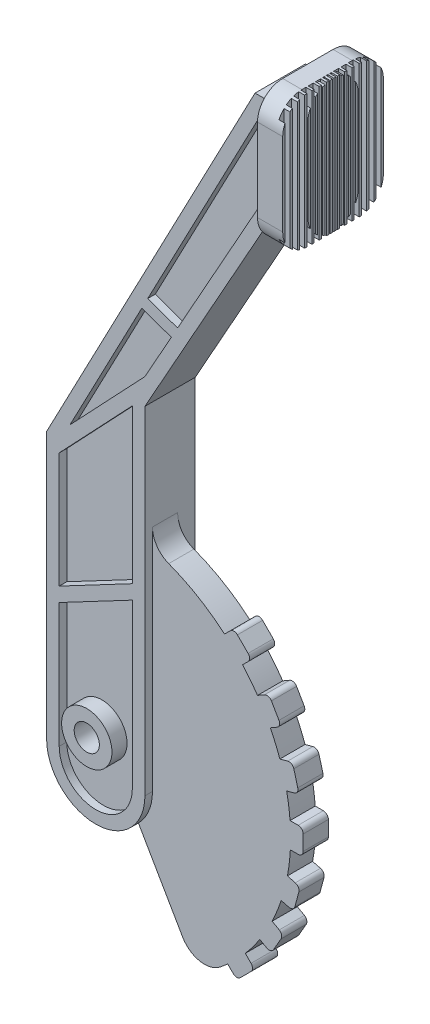
SolidWorks part; units mm, degrees
material "AISI Type 316L stainless steel"
ref_plane "Front Plane" through (0, 0, 0) normal (0, 0, 1) x (1, 0, 0)
ref_plane "Top Plane" through (0, 0, 0) normal (0, 1, 0) x (1, 0, 0)
ref_plane "Right Plane" through (0, 0, 0) normal (1, 0, 0) x (0, 0, -1)
sketch "Sketch1" plane through (0, 0, 0) normal (0, 0, 1) x (1, 0, 0)
  line L0 (0, 0) -> (0, 31.82)
  line L1 (0, 31.82) -> (-10.99, 31.82)
  line L2 (-93.795, -231.86) -> (-54.745, -231.86) construction
  line L3 (-93.795, -231.86) -> (-93.795, -126.01)
  line L4 (-93.795, -126.01) -> (-10.99, 31.82)
  line L5 (-54.745, -231.86) -> (-54.745, -97.84)
  line L6 (-54.745, -97.84) -> (0, 0)
  arc A0 (-93.795, -231.86) -> (-54.745, -231.86) centre (-74.27, -231.86) ccw
  dimension "D3" = 39.05
  dimension "D1" = 10.99
  dimension "D2" = 31.82
  dimension "D4" = 105.85
  dimension "D5" = 134.02
  dimension "D6" = 231.86
  dimension "D7" = 74.27
extrude "Boss-Extrude1" add sketch "Sketch1" along normal blind 10
sketch "Sketch2" plane through (0, 0, 0) normal (1, 0, 0) x (0, 0, -1)
  line L0 (-5, 0) -> (-5, 31.82) construction
  line L1 (-10, 0) -> (0, 0) construction
  line L2 (-10, 31.82) -> (0, 31.82) construction
  line L3 (-10, 15.91) -> (0, 15.91) construction
  line L4 (-10, 0) -> (-10, 31.82) construction
  line L5 (0, 0) -> (0, 31.82) construction
  line L7 (-10, -10.515) -> (0, -10.515)
  line L8 (-20, -0.515) -> (-20, 32.335)
  line L9 (-10, 42.335) -> (0, 42.335)
  line L10 (10, -0.515) -> (10, 32.335)
  line L11 (-20, -10.515) -> (10, 42.335) construction
  line L12 (-20, 42.335) -> (10, -10.515) construction
  arc A0 (0, -10.515) -> (10, -0.515) centre (0, -0.515) ccw
  arc A1 (-20, 32.335) -> (-10, 42.335) centre (-10, 32.335) cw
  arc A2 (-10, -10.515) -> (-20, -0.515) centre (-10, -0.515) cw
  arc A3 (0, 42.335) -> (10, 32.335) centre (0, 32.335) cw
  point P12 (-5, 15.91)
  point P29 (-5, -10.515)
  dimension "D1" = 10
  dimension "D2" = 52.85
  dimension "D3" = 30
extrude "Boss-Extrude2" add sketch "Sketch2" along normal blind 10
sketch "Sketch3" plane through (0, -10.515, 0) normal (0, -1, 0) x (1, 0, 0)
  line L0 (7.63, -4.1) -> (11.13, -4.1)
  line L1 (7.63, -7) -> (11.13, -7)
  line L2 (7.63, -7) -> (7.63, -9)
  line L3 (7.63, -9) -> (11.13, -9)
  line L4 (11.13, -7) -> (11.13, -9)
  line L5 (7.63, -7) -> (11.13, -9) construction
  line L6 (7.63, -9) -> (11.13, -7) construction
  line L7 (11.13, -4.1) -> (11.13, -6.1)
  line L8 (7.63, -6.1) -> (11.13, -6.1)
  line L9 (7.63, -4.1) -> (7.63, -6.1)
  line L10 (7.63, -1.2) -> (11.13, -1.2)
  line L11 (11.13, -1.2) -> (11.13, -3.2)
  line L12 (7.63, -3.2) -> (11.13, -3.2)
  line L13 (7.63, -1.2) -> (7.63, -3.2)
  line L14 (7.63, 1.7) -> (11.13, 1.7)
  line L15 (11.13, 1.7) -> (11.13, -0.3)
  line L16 (7.63, -0.3) -> (11.13, -0.3)
  line L17 (7.63, 1.7) -> (7.63, -0.3)
  line L18 (7.63, 4.6) -> (11.13, 4.6)
  line L19 (11.13, 4.6) -> (11.13, 2.6)
  line L20 (7.63, 2.6) -> (11.13, 2.6)
  line L21 (7.63, 4.6) -> (7.63, 2.6)
  line L22 (7.63, 7.5) -> (11.13, 7.5)
  line L23 (11.13, 7.5) -> (11.13, 5.5)
  line L24 (7.63, 5.5) -> (11.13, 5.5)
  line L25 (7.63, 7.5) -> (7.63, 5.5)
  line L26 (7.63, 10.4) -> (11.13, 10.4)
  line L27 (11.13, 10.4) -> (11.13, 8.4)
  line L28 (7.63, 8.4) -> (11.13, 8.4)
  line L29 (7.63, 10.4) -> (7.63, 8.4)
  line L30 (7.63, 13.3) -> (11.13, 13.3)
  line L31 (11.13, 13.3) -> (11.13, 11.3)
  line L32 (7.63, 11.3) -> (11.13, 11.3)
  line L33 (7.63, 13.3) -> (7.63, 11.3)
  line L34 (7.63, 16.2) -> (11.13, 16.2)
  line L35 (11.13, 16.2) -> (11.13, 14.2)
  line L36 (7.63, 14.2) -> (11.13, 14.2)
  line L37 (7.63, 16.2) -> (7.63, 14.2)
  line L38 (7.63, 19.1) -> (11.13, 19.1)
  line L39 (11.13, 19.1) -> (11.13, 17.1)
  line L40 (7.63, 17.1) -> (11.13, 17.1)
  line L41 (7.63, 19.1) -> (7.63, 17.1)
  point P0 (9.38, -8)
  dimension "D1" = 2
  dimension "D2" = 2.37
  dimension "D3" = 3.5
  dimension "D4" = 1
  dimension "D5" = 10
extrude "Cut-Extrude1" cut sketch "Sketch3" against normal through all
sketch "Sketch4" plane through (0, 0, 10) normal (0, 0, 1) x (1, 0, 0)
  line L0 (-7.9669, 26.82) -> (-53.6095, -60.1768)
  line L1 (-88.795, -130.8797) -> (-88.795, -176.7233)
  line L2 (-59.745, -231.86) -> (-59.745, -167.0258)
  line L3 (-54.7632, -87.6329) -> (-44.2444, -68.8336)
  line L4 (-5, 1.3037) -> (-5, 26.82)
  line L5 (-5, 26.82) -> (-7.9669, 26.82)
  line L6 (-54.745, -97.84) -> (0, 0)
  line L7 (0, 0) -> (0, 31.82)
  line L8 (0, 31.82) -> (-10.99, 31.82)
  line L9 (-10.99, 31.82) -> (-93.795, -126.01)
  line L10 (-93.795, -126.01) -> (-93.795, -231.86)
  line L11 (-54.745, -231.86) -> (-54.745, -97.84)
  line L12 (-54.745, -97.84) -> (0, 0)
  line L13 (0, 0) -> (0, 31.82)
  line L14 (0, 31.82) -> (-10.99, 31.82)
  line L15 (-10.99, 31.82) -> (-93.795, -126.01)
  line L16 (-93.795, -126.01) -> (-93.795, -231.86)
  line L17 (-54.745, -231.86) -> (-54.745, -97.84)
  line L18 (-41.7685, -64.4088) -> (-5, 1.3037)
  line L19 (-55.9553, -64.6481) -> (-43.8478, -68.9754)
  line L20 (-53.6095, -60.1768) -> (-41.7685, -64.4088)
  line L21 (-59.745, -96.5363) -> (-5, 1.3037) construction
  line L23 (-55.9553, -64.6481) -> (-84.5106, -119.0757)
  line L24 (-7.9669, 26.82) -> (-88.795, -127.242) construction
  line L25 (-59.745, -161.3705) -> (-59.745, -100.174)
  line L26 (-88.795, -130.8797) -> (-59.745, -100.174)
  line L27 (-59.745, -161.3705) -> (-88.795, -176.7233)
  line L28 (-84.5106, -119.0757) -> (-54.7632, -87.6329)
  line L29 (-59.745, -167.0258) -> (-88.795, -182.3787)
  line L32 (-59.745, -231.86) -> (-59.745, -96.5363) construction
  line L34 (-88.795, -182.3787) -> (-88.795, -231.86)
  line L35 (-88.795, -127.242) -> (-88.795, -231.86) construction
  arc A0 (-88.795, -231.86) -> (-59.745, -231.86) centre (-74.27, -231.86) ccw
  arc A1 (-93.795, -231.86) -> (-54.745, -231.86) centre (-74.27, -231.86) ccw
  arc A2 (-93.795, -231.86) -> (-54.745, -231.86) centre (-74.27, -231.86) ccw
  dimension "D1" = 0
  dimension "D2" = 5
extrude "Cut-Extrude2" cut sketch "Sketch4" against normal blind 3 contours L27 L25 L26 L1 | L34 A0 L2 L29 | L23 L28 L3 L19 | L0 L20 L18 L4 L5
sketch "Sketch6" plane through (0, 0, 7) normal (0, 0, 1) x (1, 0, 0)
  circle A0 centre (-74.851, -220.3715) radius 10
  circle A1 centre (-74.851, -220.3715) radius 5
  dimension "D1" = 20
  dimension "D2" = 10
extrude "Boss-Extrude3" add sketch "Sketch6" along normal blind 6
sketch "Sketch7" plane through (0, 0, 7) normal (0, 0, 1) x (1, 0, 0)
  circle A1 centre (-74.851, -220.3715) radius 5
  circle A2 centre (-74.851, -220.3715) radius 5
  dimension "D1" = 0
extrude "Boss-Extrude4" add sketch "Sketch7" against normal through all
sketch "Sketch8" plane through (0, 0, 7) normal (0, 0, 1) x (1, 0, 0)
  circle A1 centre (-74.851, -220.3715) radius 5
  circle A2 centre (-74.851, -220.3715) radius 5
  dimension "D1" = 0
extrude "Cut-Extrude3" cut sketch "Sketch8" against normal through all
ref_plane "Plane1" through (0, 0, 0) normal (0, 0, -1) x (-1, 0, 0)
mirror "Mirror2" about plane through (0, 0, 0) normal (0, 0, -1) of bodies 107 108
sketch "Sketch9" plane through (0, 0, 7) normal (0, 0, 1) x (1, 0, 0)
  line L0 (-74.851, -145.3715) -> (-74.851, -220.3715)
  line L1 (-74.851, -220.3715) -> (-37.351, -285.3234)
  arc A0 (-37.351, -285.3234) -> (-74.851, -145.3715) centre (-74.851, -220.3715) ccw
  dimension "D1" = 150
  dimension "D2" = 150
extrude "Boss-Extrude5" add sketch "Sketch9" against normal blind 10
fillet "Fillet1" radius 10 2 edges at (-54.745, -148.1167, 2) (-37.351, -285.3234, 2)
sketch "Sketch13" plane through (0, 0, 13) normal (0, 0, 1) x (1, 0, 0)
  circle A0 centre (-74.851, -220.3715) radius 5
  circle A1 centre (-74.851, -220.3715) radius 10
  circle A2 centre (-74.851, -220.3715) radius 10
  circle M3 centre (-74.851, -220.3715) radius 5
  dimension "D1" = 0
extrude "Cut-Extrude4" cut sketch "Sketch13" against normal through all contours M3
sketch "Sketch14" plane through (0, 0, 7) normal (0, 0, 1) x (1, 0, 0)
  line L0 (-74.851, -220.3715) -> (0.1445, -219.5457) construction
  line L2 (-4.8555, -214.5457) -> (3.1445, -214.5457)
  line L3 (-4.8555, -214.5457) -> (-4.8555, -224.5457)
  line L4 (-4.8555, -224.5457) -> (3.1445, -224.5457)
  line L5 (5.1445, -216.5457) -> (5.1445, -222.5457)
  line L6 (-4.8555, -214.5457) -> (5.1445, -224.5457) construction
  line L7 (-4.8555, -224.5457) -> (5.1445, -214.5457) construction
  arc A0 (-27.8048, -278.7809) -> (-48.2869, -150.2334) centre (-74.851, -220.3715) ccw construction
  arc A1 (3.1445, -224.5457) -> (5.1445, -222.5457) centre (3.1445, -222.5457) ccw
  arc A2 (3.1445, -214.5457) -> (5.1445, -216.5457) centre (3.1445, -216.5457) cw
  dimension "D3" = 2
  dimension "D1" = 10
  dimension "D2" = 10
extrude "Boss-Extrude6" add sketch "Sketch14" against normal blind 10
pattern_circular "CirPattern1" count 4 over 45 about axis through (-74.851, -220.3715, 0) along (0, 0, 1) of "Boss-Extrude6"
pattern_circular "CirPattern2" count 4 over 45 about axis through (-74.851, -220.3715, 0) along (0, 0, 1) of "Boss-Extrude6"
